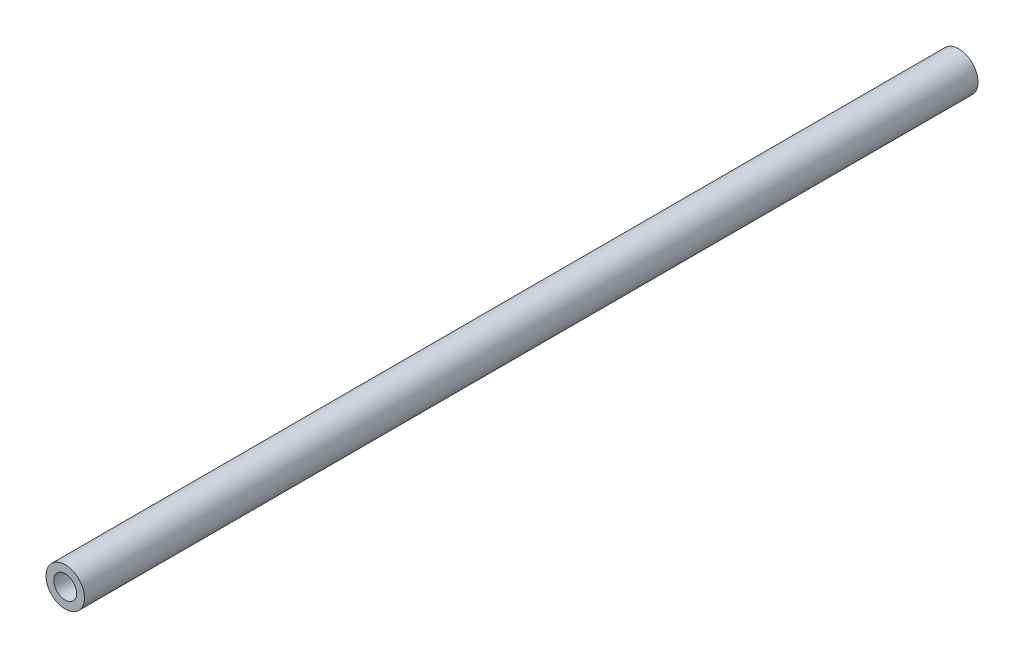
SolidWorks part; units mm, degrees
ref_plane "Front Plane" through (0, 0, 0) normal (0, 0, 1) x (1, 0, 0)
ref_plane "Top Plane" through (0, 0, 0) normal (0, 1, 0) x (1, 0, 0)
ref_plane "Right Plane" through (0, 0, 0) normal (1, 0, 0) x (0, 0, -1)
sketch "Sketch1" plane through (0, 0, 0) normal (0, 0, 1) x (1, 0, 0)
  circle A0 centre (0, 0) radius 4.7
  circle A1 centre (0, 0) radius 7.9
  dimension "D1" = 15.8
  dimension "D2" = 3.2
extrude "Boss-Extrude1" add sketch "Sketch1" along normal blind 366.7
